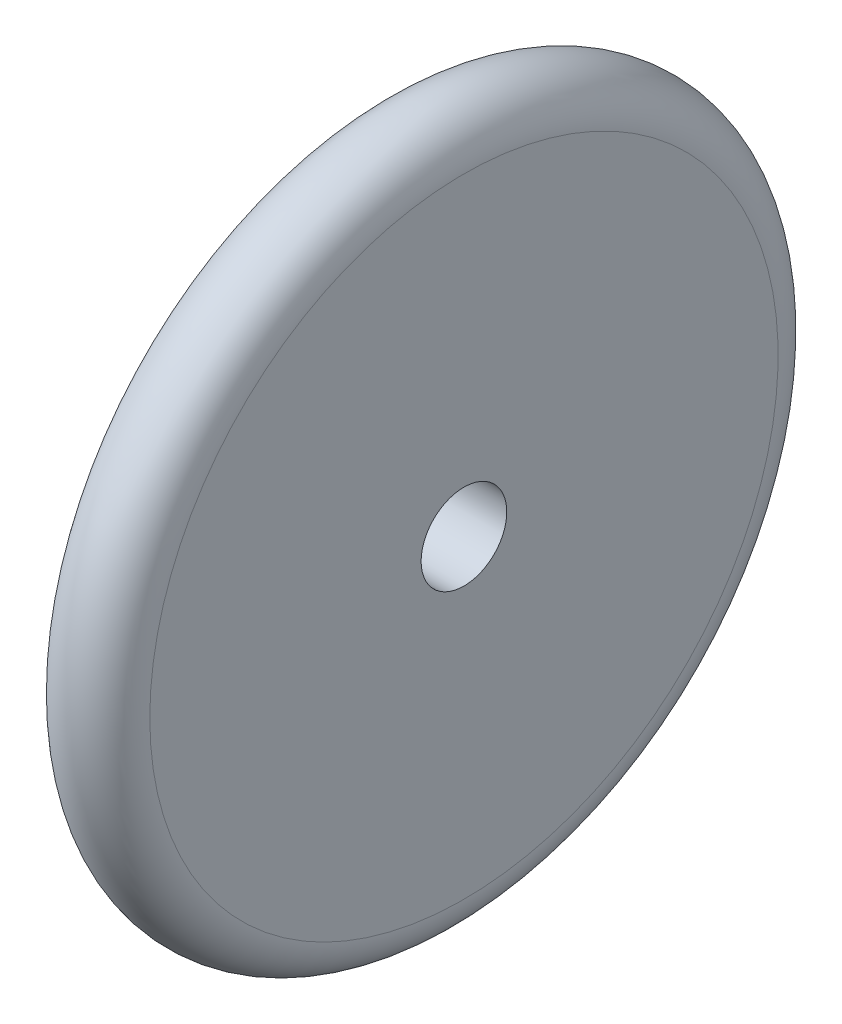
SolidWorks part; units mm, degrees
ref_plane "Front Plane" through (0, 0, 0) normal (0, 0, 1) x (1, 0, 0)
ref_plane "Top Plane" through (0, 0, 0) normal (0, 1, 0) x (1, 0, 0)
ref_plane "Right Plane" through (0, 0, 0) normal (1, 0, 0) x (0, 0, -1)
sketch "Sketch1" plane through (0, 0, 0) normal (0, 0, 1) x (1, 0, 0)
  line L0 (0, 0) -> (30, 0)
  line L2 (0, 15) -> (30, 15)
  line L3 (0, 15) -> (0, 110)
  line L5 (30, 15) -> (30, 110)
  arc A0 (0, 110) -> (30, 110) centre (15, 110) cw
  point P8 (15, 125)
  point P9 (0, 0)
  dimension "D1" = 30
  dimension "D2" = 15
  dimension "D3" = 125
revolve "Revolve1" add sketch "Sketch1" angle 360 about L0
